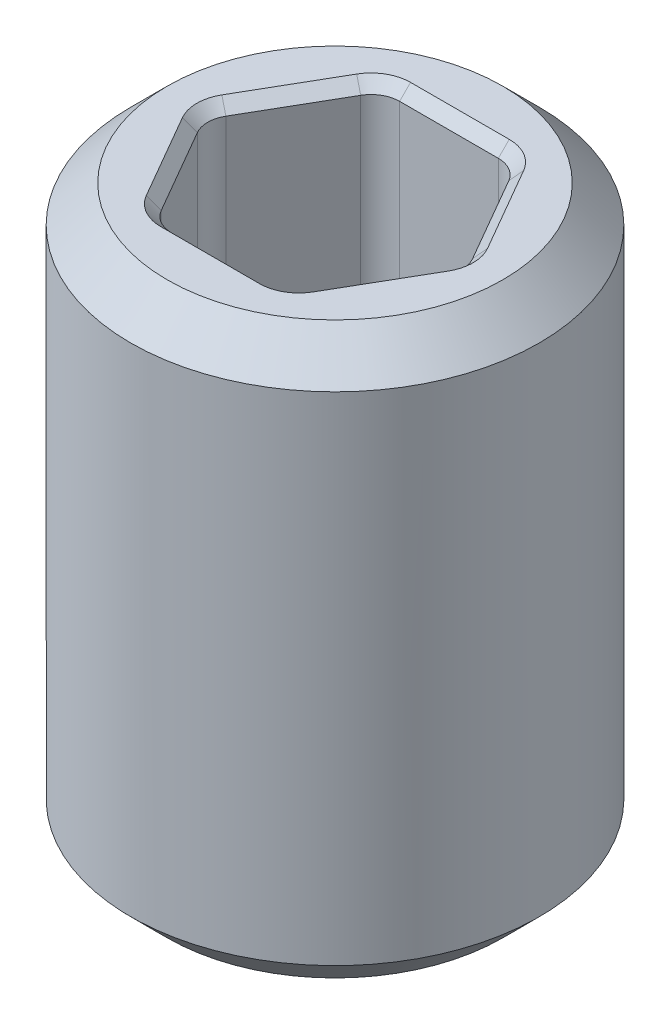
SolidWorks part; units mm, degrees
ref_plane "Front Plane" through (0, 0, 0) normal (0, 0, 1) x (1, 0, 0)
ref_plane "Top Plane" through (0, 0, 0) normal (0, 1, 0) x (1, 0, 0)
ref_plane "Right Plane" through (0, 0, 0) normal (1, 0, 0) x (0, 0, -1)
sketch "Sketch1" plane through (0, 0, 0) normal (0, 0, 1) x (1, 0, 0)
  line L0 (0, -1.7042) -> (0, -1.1626) construction
  line L1 (1.4224, -1.9844) -> (1.4224, 1.9844)
  line L2 (1.4224, 1.9844) -> (0, 1.9844)
  line L3 (0, 1.9844) -> (0, -1.9844)
  line L4 (0, -1.9844) -> (1.4224, -1.9844)
  dimension "D1" = 3.9688
  dimension "D2" = 2.8448
revolve "Revolve1" add sketch "Sketch1" angle 360 about L0
sketch "Sketch3" plane through (0, 0, 0) normal (0, 1, 0) x (1, 0, 0)
  line L1 (0.9165, 0) -> (0.4583, 0.7938)
  line L2 (0.4583, 0.7938) -> (-0.4583, 0.7937)
  line L3 (-0.4583, 0.7937) -> (-0.9165, 0)
  line L4 (-0.9165, 0) -> (-0.4583, -0.7938)
  line L5 (-0.4583, -0.7938) -> (0.4583, -0.7937)
  line L6 (0.4583, -0.7937) -> (0.9165, 0)
  circle A0 centre (0, 0) radius 0.7937 construction
  dimension "D1" = 1.5875
extrude "Cut-Extrude1" cut sketch "Sketch3" against normal through all both and the other way through all contours L2 L3 L4 L5 L6 L1
fillet "Fillet1" radius 0.1984 6 edges at (0.4583, 0, -0.7938) (0.9165, 0, 0) (0.4583, 0, 0.7937) (-0.4583, 0, 0.7938) (-0.9165, 0, 0) (-0.4583, 0, -0.7937)
chamfer "Chamfer1" distance 0.254 angle 45 2 edges at (0, -1.9844, -1.4224) (0, 1.9844, -1.4224)
chamfer "Chamfer2" distance 0.0762 angle 45 24 edges at (0.6874, 1.9844, -0.3969) (0.4429, 1.9844, -0.7672) (0.8858, 1.9844, 0) (0, 1.9844, -0.7937) (0.6874, 1.9844, 0.3969) (-0.4429, 1.9844, -0.7672) (0.4429, 1.9844, 0.7672) (-0.6874, 1.9844, -0.3969) (0, 1.9844, 0.7937) (-0.8858, 1.9844, 0) (-0.4429, 1.9844, 0.7672) (-0.6874, 1.9844, 0.3969) (0.6874, -1.9844, 0.3969) (0.8858, -1.9844, 0) (0.4429, -1.9844, 0.7672) (0.6874, -1.9844, -0.3969) (0, -1.9844, 0.7937) (0.4429, -1.9844, -0.7672) (-0.4429, -1.9844, 0.7672) (0, -1.9844, -0.7937) (-0.6874, -1.9844, 0.3969) (-0.4429, -1.9844, -0.7672) (-0.8858, -1.9844, 0) (-0.6874, -1.9844, -0.3969)
